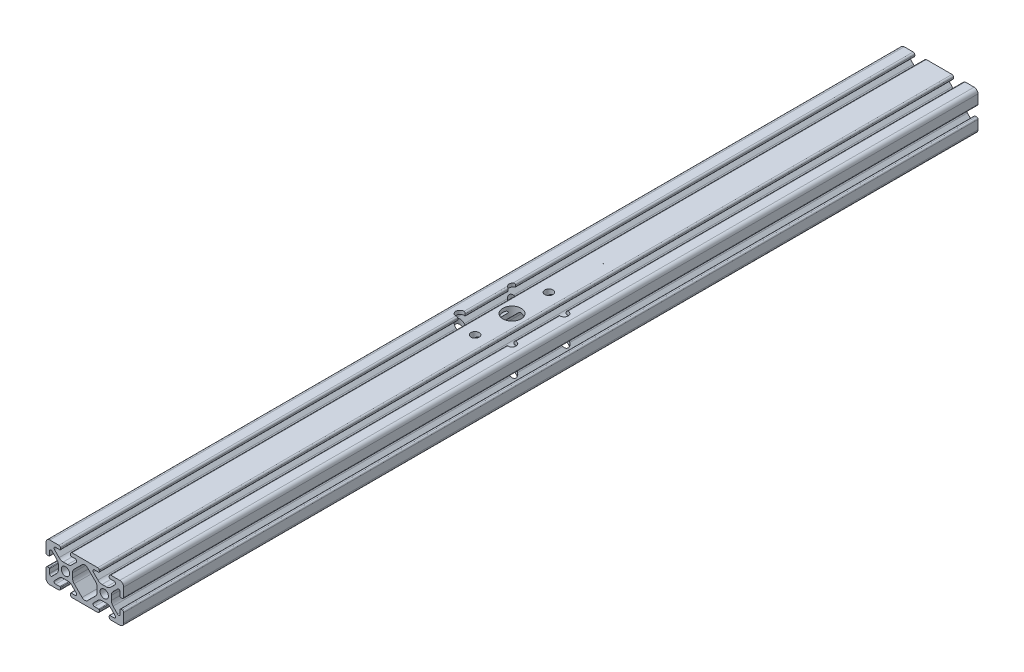
SolidWorks part; units mm, degrees
ref_plane "Ebene vorne" through (0, 0, 0) normal (0, 0, 1) x (1, 0, 0)
ref_plane "Ebene oben" through (0, 0, 0) normal (0, 1, 0) x (1, 0, 0)
ref_plane "Ebene rechts" through (0, 0, 0) normal (1, 0, 0) x (0, 0, -1)
ref_plane "Ebene1" through (0, 0, 1000) normal (0, 0, 1) x (1, 0, 0)
sketch "Skizze1" plane through (0, 0, 1000) normal (0, 0, 1) x (1, 0, 0)
  line L0 (12.975, -8.8654) -> (12.975, -11.1346)
  line L1 (12.0963, -13.2559) -> (8.0392, -17.313)
  line L2 (5.2108, -17.313) -> (1.1537, -13.2559)
  line L3 (0.275, -11.1346) -> (0.275, -8.8654)
  line L4 (1.1537, -6.7441) -> (5.2108, -2.687)
  line L5 (8.0392, -2.687) -> (12.0963, -6.7441)
  line L6 (24.825, -12.875) -> (24.825, -15.0441)
  line L7 (23.4935, -15.5957) -> (21.1537, -13.2559)
  line L8 (20.275, -11.1346) -> (20.275, -8.8654)
  line L9 (21.1537, -6.7441) -> (23.4935, -4.4043)
  line L10 (24.825, -4.9559) -> (24.825, -7.125)
  line L11 (25.125, -7.425) -> (25.825, -7.425)
  line L12 (26.625, -6.625) -> (26.625, -2)
  line L13 (24.625, 0) -> (20, 0)
  line L14 (19.2, -0.8) -> (19.2, -1.5)
  line L15 (19.5, -1.8) -> (21.6691, -1.8)
  line L16 (22.2207, -3.1315) -> (19.8809, -5.4713)
  line L17 (17.7596, -6.35) -> (15.4904, -6.35)
  line L18 (13.3691, -5.4713) -> (11.0293, -3.1315)
  line L19 (11.5809, -1.8) -> (13.75, -1.8)
  line L20 (14.05, -1.5) -> (14.05, -0.8)
  line L21 (13.25, 0) -> (0, 0)
  line L22 (-0.8, -0.8) -> (-0.8, -1.5)
  line L23 (-0.5, -1.8) -> (1.6691, -1.8)
  line L24 (2.2207, -3.1315) -> (-0.1191, -5.4713)
  line L25 (-2.2404, -6.35) -> (-4.5096, -6.35)
  line L26 (-6.6309, -5.4713) -> (-8.9707, -3.1315)
  line L27 (-8.4191, -1.8) -> (-6.25, -1.8)
  line L28 (-5.95, -1.5) -> (-5.95, -0.8)
  line L29 (-6.75, 0) -> (-11.375, 0)
  line L30 (-13.375, -2) -> (-13.375, -6.625)
  line L31 (-12.575, -7.425) -> (-11.875, -7.425)
  line L32 (-11.575, -7.125) -> (-11.575, -4.9559)
  line L33 (-10.2435, -4.4043) -> (-7.9037, -6.7441)
  line L34 (-7.025, -8.8654) -> (-7.025, -11.1346)
  line L35 (-7.9037, -13.2559) -> (-10.2435, -15.5957)
  line L36 (-11.575, -15.0441) -> (-11.575, -12.875)
  line L37 (-11.875, -12.575) -> (-12.575, -12.575)
  line L38 (-13.375, -13.375) -> (-13.375, -18)
  line L39 (-11.375, -20) -> (-6.75, -20)
  line L40 (-5.95, -19.2) -> (-5.95, -18.5)
  line L41 (-6.25, -18.2) -> (-8.4191, -18.2)
  line L42 (-8.9707, -16.8685) -> (-6.6309, -14.5287)
  line L43 (-4.5096, -13.65) -> (-2.2404, -13.65)
  line L44 (-0.1191, -14.5287) -> (2.2207, -16.8685)
  line L45 (1.6691, -18.2) -> (-0.5, -18.2)
  line L46 (-0.8, -18.5) -> (-0.8, -19.2)
  line L47 (0, -20) -> (13.25, -20)
  line L48 (14.05, -19.2) -> (14.05, -18.5)
  line L49 (13.75, -18.2) -> (11.5809, -18.2)
  line L50 (11.0293, -16.8685) -> (13.3691, -14.5287)
  line L51 (15.4904, -13.65) -> (17.7596, -13.65)
  line L52 (19.8809, -14.5287) -> (22.2207, -16.8685)
  line L53 (21.6691, -18.2) -> (19.5, -18.2)
  line L54 (19.2, -18.5) -> (19.2, -19.2)
  line L55 (20, -20) -> (24.625, -20)
  line L56 (26.625, -18) -> (26.625, -13.375)
  line L57 (25.825, -12.575) -> (25.125, -12.575)
  circle A0 centre (-3.375, -10) radius 2.15
  circle A1 centre (16.625, -10) radius 2.15
  arc A2 (12.0963, -6.7441) -> (12.975, -8.8654) centre (9.975, -8.8654) cw
  arc A3 (12.975, -11.1346) -> (12.0963, -13.2559) centre (9.975, -11.1346) cw
  arc A4 (8.0392, -17.313) -> (5.2108, -17.313) centre (6.625, -15.8988) cw
  arc A5 (1.1537, -13.2559) -> (0.275, -11.1346) centre (3.275, -11.1346) cw
  arc A6 (0.275, -8.8654) -> (1.1537, -6.7441) centre (3.275, -8.8654) cw
  arc A7 (5.2108, -2.687) -> (8.0392, -2.687) centre (6.625, -4.1012) cw
  arc A8 (24.825, -15.0441) -> (23.4935, -15.5957) centre (24.045, -15.0441) cw
  arc A9 (21.1537, -13.2559) -> (20.275, -11.1346) centre (23.275, -11.1346) cw
  arc A10 (20.275, -8.8654) -> (21.1537, -6.7441) centre (23.275, -8.8654) cw
  arc A11 (23.4935, -4.4043) -> (24.825, -4.9559) centre (24.045, -4.9559) cw
  arc A12 (24.825, -7.125) -> (25.125, -7.425) centre (25.125, -7.125) ccw
  arc A13 (25.825, -7.425) -> (26.625, -6.625) centre (25.825, -6.625) ccw
  arc A14 (26.625, -2) -> (24.625, 0) centre (24.625, -2) ccw
  arc A15 (20, 0) -> (19.2, -0.8) centre (20, -0.8) ccw
  arc A16 (19.2, -1.5) -> (19.5, -1.8) centre (19.5, -1.5) ccw
  arc A17 (21.6691, -1.8) -> (22.2207, -3.1315) centre (21.6691, -2.58) cw
  arc A18 (19.8809, -5.4713) -> (17.7596, -6.35) centre (17.7596, -3.35) cw
  arc A19 (15.4904, -6.35) -> (13.3691, -5.4713) centre (15.4904, -3.35) cw
  arc A20 (11.0293, -3.1315) -> (11.5809, -1.8) centre (11.5809, -2.58) cw
  arc A21 (13.75, -1.8) -> (14.05, -1.5) centre (13.75, -1.5) ccw
  arc A22 (14.05, -0.8) -> (13.25, 0) centre (13.25, -0.8) ccw
  arc A23 (0, 0) -> (-0.8, -0.8) centre (0, -0.8) ccw
  arc A24 (-0.8, -1.5) -> (-0.5, -1.8) centre (-0.5, -1.5) ccw
  arc A25 (1.6691, -1.8) -> (2.2207, -3.1315) centre (1.6691, -2.58) cw
  arc A26 (-0.1191, -5.4713) -> (-2.2404, -6.35) centre (-2.2404, -3.35) cw
  arc A27 (-4.5096, -6.35) -> (-6.6309, -5.4713) centre (-4.5096, -3.35) cw
  arc A28 (-8.9707, -3.1315) -> (-8.4191, -1.8) centre (-8.4191, -2.58) cw
  arc A29 (-6.25, -1.8) -> (-5.95, -1.5) centre (-6.25, -1.5) ccw
  arc A30 (-5.95, -0.8) -> (-6.75, 0) centre (-6.75, -0.8) ccw
  arc A31 (-11.375, 0) -> (-13.375, -2) centre (-11.375, -2) ccw
  arc A32 (-13.375, -6.625) -> (-12.575, -7.425) centre (-12.575, -6.625) ccw
  arc A33 (-11.875, -7.425) -> (-11.575, -7.125) centre (-11.875, -7.125) ccw
  arc A34 (-11.575, -4.9559) -> (-10.2435, -4.4043) centre (-10.795, -4.9559) cw
  arc A35 (-7.9037, -6.7441) -> (-7.025, -8.8654) centre (-10.025, -8.8654) cw
  arc A36 (-7.025, -11.1346) -> (-7.9037, -13.2559) centre (-10.025, -11.1346) cw
  arc A37 (-10.2435, -15.5957) -> (-11.575, -15.0441) centre (-10.795, -15.0441) cw
  arc A38 (-11.575, -12.875) -> (-11.875, -12.575) centre (-11.875, -12.875) ccw
  arc A39 (-12.575, -12.575) -> (-13.375, -13.375) centre (-12.575, -13.375) ccw
  arc A40 (-13.375, -18) -> (-11.375, -20) centre (-11.375, -18) ccw
  arc A41 (-6.75, -20) -> (-5.95, -19.2) centre (-6.75, -19.2) ccw
  arc A42 (-5.95, -18.5) -> (-6.25, -18.2) centre (-6.25, -18.5) ccw
  arc A43 (-8.4191, -18.2) -> (-8.9707, -16.8685) centre (-8.4191, -17.42) cw
  arc A44 (-6.6309, -14.5287) -> (-4.5096, -13.65) centre (-4.5096, -16.65) cw
  arc A45 (-2.2404, -13.65) -> (-0.1191, -14.5287) centre (-2.2404, -16.65) cw
  arc A46 (2.2207, -16.8685) -> (1.6691, -18.2) centre (1.6691, -17.42) cw
  arc A47 (-0.5, -18.2) -> (-0.8, -18.5) centre (-0.5, -18.5) ccw
  arc A48 (-0.8, -19.2) -> (0, -20) centre (0, -19.2) ccw
  arc A49 (13.25, -20) -> (14.05, -19.2) centre (13.25, -19.2) ccw
  arc A50 (14.05, -18.5) -> (13.75, -18.2) centre (13.75, -18.5) ccw
  arc A51 (11.5809, -18.2) -> (11.0293, -16.8685) centre (11.5809, -17.42) cw
  arc A52 (13.3691, -14.5287) -> (15.4904, -13.65) centre (15.4904, -16.65) cw
  arc A53 (17.7596, -13.65) -> (19.8809, -14.5287) centre (17.7596, -16.65) cw
  arc A54 (22.2207, -16.8685) -> (21.6691, -18.2) centre (21.6691, -17.42) cw
  arc A55 (19.5, -18.2) -> (19.2, -18.5) centre (19.5, -18.5) ccw
  arc A56 (19.2, -19.2) -> (20, -20) centre (20, -19.2) ccw
  arc A57 (24.625, -20) -> (26.625, -18) centre (24.625, -18) ccw
  arc A58 (26.625, -13.375) -> (25.825, -12.575) centre (25.825, -13.375) ccw
  arc A59 (25.125, -12.575) -> (24.825, -12.875) centre (25.125, -12.875) ccw
extrude "Aufsatz-Linear austragen1" add sketch "Skizze1" against normal blind 440
sketch "Skizze2" plane through (0, 0, 0) normal (0, 1, 0) x (1, 0, 0)
  line L0 (0, -780) -> (13.25, -780) construction
  line L1 (0, -560) -> (0, -1000) construction
  line L2 (13.25, -560) -> (13.25, -1000) construction
  circle A0 centre (6.625, -780) radius 4.7473
extrude "Schnitt-Linear austragen1" cut sketch "Skizze2" against normal through all
hole_wizard "M5 Gewindebohrung1" positions "Skizze3" profile "Skizze4" tap size "M5" standard "DIN" end condition through all
sketch "Skizze3" plane through (0, -20, 0) normal (0, -1, 0) x (-1, 0, 0)
  point P0 (-6.625, -799)
  point P3 (-20.06, -793.435)
  point P6 (6.81, -793.435)
  point P9 (-6.625, -761)
  point P12 (-20.06, -766.565)
  point P15 (5.2413, -767.4856)
sketch "Skizze4" plane through (6.625, -20, 799) normal (1, 0, 0) x (0, 0, -1)
  line L0 (0, 0) -> (0, 20)
  line L1 (0, 20) -> (2.1, 20)
  line L2 (2.1, 20) -> (2.1, 0)
  line L5 (2.1, 0) -> (0, 0)
  line L11 (0, -6.35) -> (0, 107.95) construction
  dimension "Bohrerdurchmesser" = 4.2
  dimension "Bohrungstiefe" = 20
cosmetic thread "Bohrungsgewinde1" parameters "D2"=5
cosmetic thread "Bohrungsgewinde3" parameters "D2"=5
cosmetic thread "Bohrungsgewinde4" parameters "D2"=5
cosmetic thread "Bohrungsgewinde5" parameters "D2"=5
cosmetic thread "Bohrungsgewinde6" parameters "D2"=5
cosmetic thread "Bohrungsgewinde7" parameters "D2"=5
